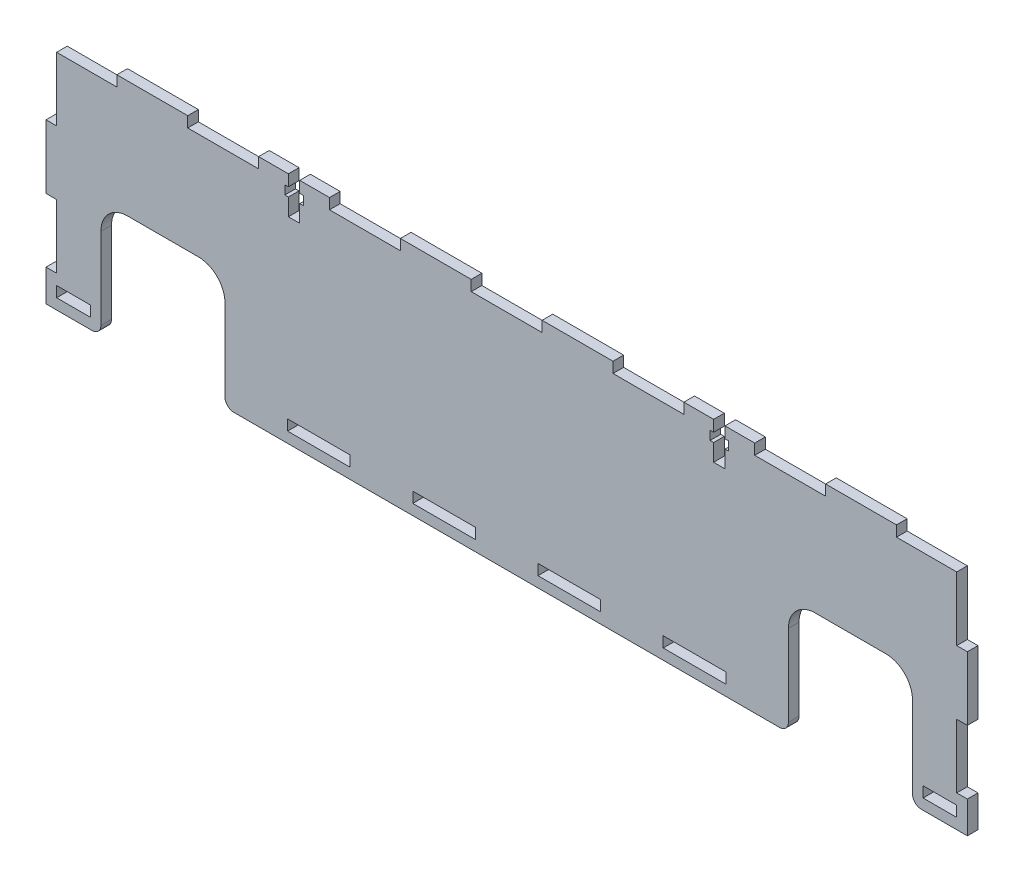
SolidWorks part; units mm, degrees
ref_plane "Front Plane" through (0, 0, 0) normal (0, 0, 1) x (1, 0, 0)
ref_plane "Top Plane" through (0, 0, 0) normal (0, 1, 0) x (1, 0, 0)
ref_plane "Right Plane" through (0, 0, 0) normal (1, 0, 0) x (0, 0, -1)
sketch "Sketch1" plane through (0, 0, 0) normal (0, 0, 1) x (1, 0, 0)
  line L0 (-130, 33) -> (130, 33)
  line L1 (130, 33) -> (130, -33)
  line L2 (130, -33) -> (114.5, -33)
  line L3 (114.5, -33) -> (114.5, 0)
  line L4 (114.5, 0) -> (79.5, 0)
  line L5 (79.5, 0) -> (79.5, -33)
  line L6 (79.5, -33) -> (-79.5, -33)
  line L7 (-79.5, -33) -> (-79.5, 0)
  line L8 (-79.5, 0) -> (-114.5, 0)
  line L9 (-114.5, 0) -> (-114.5, -33)
  line L10 (-114.5, -33) -> (-130, -33)
  line L11 (-130, -33) -> (-130, 33)
  point P14 (0, 33)
  point P15 (130, 0)
  dimension "D1" = 260
  dimension "D2" = 66
  dimension "D3" = 15.5
  dimension "D4" = 35
  dimension "D5" = 33
extrude "Boss-Extrude1" add sketch "Sketch1" along normal blind 3
sketch "Sketch2" plane through (0, 0, 3) normal (0, 0, 1) x (1, 0, 0)
  line L0 (-79.5, -30) -> (-61.8333, -30) construction
  line L1 (-61.8333, -30) -> (-44.1667, -30)
  line L2 (-61.8333, -30) -> (-61.8333, -27)
  line L3 (-61.8333, -27) -> (-44.1667, -27)
  line L4 (-44.1667, -30) -> (-44.1667, -27)
  line L5 (-61.8333, -30) -> (-44.1667, -27) construction
  line L6 (-61.8333, -27) -> (-44.1667, -30) construction
  line L7 (-26.5, -30) -> (-8.8333, -30)
  line L8 (-26.5, -30) -> (-26.5, -27)
  line L9 (-26.5, -27) -> (-8.8333, -27)
  line L10 (-8.8333, -30) -> (-8.8333, -27)
  line L11 (-26.5, -30) -> (-8.8333, -27) construction
  line L12 (-26.5, -27) -> (-8.8333, -30) construction
  line L13 (8.8333, -30) -> (26.5, -30)
  line L14 (8.8333, -30) -> (8.8333, -27)
  line L15 (8.8333, -27) -> (26.5, -27)
  line L16 (26.5, -30) -> (26.5, -27)
  line L17 (8.8333, -30) -> (26.5, -27) construction
  line L18 (8.8333, -27) -> (26.5, -30) construction
  line L19 (44.1667, -30) -> (61.8333, -30)
  line L20 (44.1667, -30) -> (44.1667, -27)
  line L21 (44.1667, -27) -> (61.8333, -27)
  line L22 (61.8333, -30) -> (61.8333, -27)
  line L23 (44.1667, -30) -> (61.8333, -27) construction
  line L24 (44.1667, -27) -> (61.8333, -30) construction
  line L25 (-79.5, 0) -> (-79.5, -33) construction
  line L26 (-44.1667, -30) -> (-26.5, -30) construction
  line L27 (-8.8333, -30) -> (8.8333, -30) construction
  line L28 (26.5, -30) -> (44.1667, -30) construction
  line L29 (61.8333, -30) -> (79.5, -30) construction
  line L30 (79.5, -33) -> (79.5, 0) construction
  line L31 (-79.5, -33) -> (79.5, -33) construction
  line L32 (114.5, -33) -> (130, -33) construction
  line L33 (-127, -30) -> (-117.5, -30)
  line L34 (-127, -30) -> (-127, -27)
  line L35 (-127, -27) -> (-117.5, -27)
  line L36 (-117.5, -30) -> (-117.5, -27)
  line L37 (-127, -30) -> (-117.5, -27) construction
  line L38 (-127, -27) -> (-117.5, -30) construction
  line L39 (117.5, -30) -> (127, -30)
  line L40 (117.5, -30) -> (117.5, -27)
  line L41 (117.5, -27) -> (127, -27)
  line L42 (127, -30) -> (127, -27)
  line L43 (117.5, -30) -> (127, -27) construction
  line L44 (117.5, -27) -> (127, -30) construction
  line L45 (-130, -33) -> (-114.5, -33) construction
  line L46 (-130, 33) -> (-130, -33) construction
  line L47 (-127, -24) -> (-130, -24)
  line L48 (-127, -24) -> (-127, -6)
  line L49 (-127, -6) -> (-130, -6)
  line L50 (-130, -24) -> (-130, -6)
  line L51 (-127, -24) -> (-130, -6) construction
  line L52 (-127, -6) -> (-130, -24) construction
  line L53 (-127, -6) -> (-127, 12) construction
  line L54 (-127, 12) -> (-130, 12)
  line L55 (-127, 12) -> (-127, 30)
  line L56 (-127, 30) -> (-130, 30)
  line L57 (-130, 12) -> (-130, 30)
  line L58 (-127, 12) -> (-130, 30) construction
  line L59 (-127, 30) -> (-130, 12) construction
  line L60 (-127, 30) -> (-127, 33) construction
  line L61 (130, 33) -> (-130, 33) construction
  line L62 (-127, -24) -> (-127, -27) construction
  line L63 (130, -33) -> (130, 33) construction
  line L64 (127, 12) -> (130, 12)
  line L65 (127, 12) -> (127, 30)
  line L66 (127, 30) -> (130, 30)
  line L67 (130, 12) -> (130, 30)
  line L68 (127, 12) -> (130, 30) construction
  line L69 (127, 30) -> (130, 12) construction
  line L70 (-110, 30) -> (-90, 30) construction
  line L71 (127, -24) -> (130, -24)
  line L72 (127, -24) -> (127, -6)
  line L73 (127, -6) -> (130, -6)
  line L74 (130, -24) -> (130, -6)
  line L75 (127, -24) -> (130, -6) construction
  line L76 (127, -6) -> (130, -24) construction
  line L77 (-110, 30) -> (-130, 30)
  line L78 (-110, 30) -> (-110, 33)
  line L79 (-110, 33) -> (-130, 33)
  line L80 (-130, 30) -> (-130, 33)
  line L81 (-110, 30) -> (-130, 33) construction
  line L82 (-110, 33) -> (-130, 30) construction
  line L83 (-90, 30) -> (-70, 30)
  line L84 (-90, 30) -> (-90, 33)
  line L85 (-90, 33) -> (-70, 33)
  line L86 (-70, 30) -> (-70, 33)
  line L87 (-90, 30) -> (-70, 33) construction
  line L88 (-90, 33) -> (-70, 30) construction
  line L89 (-50, 30) -> (-30, 30)
  line L90 (-50, 30) -> (-50, 33)
  line L91 (-50, 33) -> (-30, 33)
  line L92 (-30, 30) -> (-30, 33)
  line L93 (-50, 30) -> (-30, 33) construction
  line L94 (-50, 33) -> (-30, 30) construction
  line L95 (-10, 30) -> (10, 30)
  line L96 (-10, 30) -> (-10, 33)
  line L97 (-10, 33) -> (10, 33)
  line L98 (10, 30) -> (10, 33)
  line L99 (-10, 30) -> (10, 33) construction
  line L100 (-10, 33) -> (10, 30) construction
  line L101 (30, 30) -> (50, 30)
  line L102 (30, 30) -> (30, 33)
  line L103 (30, 33) -> (50, 33)
  line L104 (50, 30) -> (50, 33)
  line L105 (30, 30) -> (50, 33) construction
  line L106 (30, 33) -> (50, 30) construction
  line L107 (70, 30) -> (90, 30)
  line L108 (70, 30) -> (70, 33)
  line L109 (70, 33) -> (90, 33)
  line L110 (90, 30) -> (90, 33)
  line L111 (70, 30) -> (90, 33) construction
  line L112 (70, 33) -> (90, 30) construction
  line L113 (110, 30) -> (130, 30)
  line L114 (110, 30) -> (110, 33)
  line L115 (110, 33) -> (130, 33)
  line L116 (130, 30) -> (130, 33)
  line L117 (110, 30) -> (130, 33) construction
  line L118 (110, 33) -> (130, 30) construction
  line L119 (-70, 30) -> (-50, 30) construction
  line L120 (-30, 30) -> (-10, 30) construction
  line L121 (10, 30) -> (30, 30) construction
  line L122 (50, 30) -> (70, 30) construction
  line L123 (90, 30) -> (110, 30) construction
  point P0 (-53, -28.5)
  point P5 (-17.6667, -28.5)
  point P10 (17.6667, -28.5)
  point P15 (53, -28.5)
  point P28 (-122.25, -28.5)
  point P33 (122.25, -28.5)
  point P38 (-128.5, -15)
  point P41 (122.25, -33)
  point P44 (-122.25, -33)
  point P51 (-128.5, 21)
  point P56 (128.5, 21)
  point P66 (128.5, -15)
  point P71 (-120, 31.5)
  point P77 (-80, 31.5)
  point P82 (-40, 31.5)
  point P87 (0, 31.5)
  point P92 (40, 31.5)
  point P97 (80, 31.5)
  point P102 (120, 31.5)
  line M15 (-130, 33) -> (-130, -33)
  line M25 (130, -33) -> (130, 33)
  line M26 (130, 33) -> (-130, 33)
  dimension "D1" = 3
  dimension "D2" = 3
  dimension "D3" = 9.5
  dimension "D4" = 3
extrude "Cut-Extrude1" cut sketch "Sketch2" against normal through all both and the other way through all contours L55 L56 L54 M15 | L48 L49 L47 M15 | L1 L4 L3 L2 | L7 L10 L9 L8 | L13 L16 L15 L14 | L19 L22 L21 L20 | L39 L42 L41 L40 | L73 L72 L71 M25 | L66 L65 L64 M25 | L114 L113 L66 M25 M26 | L107 L110 L108 M26 | L101 L104 L102 M26 | L89 L92 L90 M26 | L83 L86 L84 M26 | L95 L98 L96 M26 | L79 L80 L77 L78 | L36 L35 L34 L33
sketch "Sketch3" plane through (0, 0, 3) normal (0, 0, 1) x (1, 0, 0)
  line L0 (-50, 33) -> (-70, 33) construction
  line L1 (-61.6, 22.5) -> (-58.4, 22.5)
  line L2 (-61.6, 22.5) -> (-61.6, 33)
  line L3 (-61.6, 33) -> (-58.4, 33)
  line L4 (-58.4, 22.5) -> (-58.4, 33)
  line L5 (-61.6, 22.5) -> (-58.4, 33) construction
  line L6 (-61.6, 33) -> (-58.4, 22.5) construction
  line L7 (70, 33) -> (50, 33) construction
  line L8 (58.4, 22.5) -> (61.6, 22.5)
  line L9 (58.4, 22.5) -> (58.4, 33)
  line L10 (58.4, 33) -> (61.6, 33)
  line L11 (61.6, 22.5) -> (61.6, 33)
  line L12 (58.4, 22.5) -> (61.6, 33) construction
  line L13 (58.4, 33) -> (61.6, 22.5) construction
  line L14 (-60, 33) -> (-60, 29.825) construction
  line L15 (-62.6, 29.825) -> (-57.4, 29.825)
  line L16 (-62.6, 29.825) -> (-62.6, 27.325)
  line L17 (-62.6, 27.325) -> (-57.4, 27.325)
  line L18 (-57.4, 29.825) -> (-57.4, 27.325)
  line L19 (-62.6, 29.825) -> (-57.4, 27.325) construction
  line L20 (-62.6, 27.325) -> (-57.4, 29.825) construction
  line L21 (57.4, 29.825) -> (62.6, 29.825)
  line L22 (57.4, 29.825) -> (57.4, 27.325)
  line L23 (57.4, 27.325) -> (62.6, 27.325)
  line L24 (62.6, 29.825) -> (62.6, 27.325)
  line L25 (57.4, 29.825) -> (62.6, 27.325) construction
  line L26 (57.4, 27.325) -> (62.6, 29.825) construction
  line L27 (60, 33) -> (60, 29.825) construction
  point P0 (-60, 27.75)
  point P7 (60, 27.75)
  point P14 (60, 33)
  point P15 (-60, 33)
  point P16 (-60, 28.575)
  point P21 (60, 28.575)
  dimension "D1" = 3.2
  dimension "D2" = 10.5
  dimension "D3" = 2.5
  dimension "D4" = 5.2
  dimension "D5" = 3.175
extrude "Cut-Extrude2" cut sketch "Sketch3" against normal through all both and the other way through all contours L4 L3 L2 L1 | L18 L17 L16 L15 | L8 L11 L10 L9 | L22 L23 L24 L21
fillet "Fillet1" radius 7.5 4 edges at (114.5, 0, 1.5) (79.5, 0, 1.5) (-79.5, 0, 1.5) (-114.5, 0, 1.5)
fillet "Fillet2" radius 2.5 4 edges at (114.5, -33, 1.5) (79.5, -33, 1.5) (-79.5, -33, 1.5) (-114.5, -33, 1.5)
